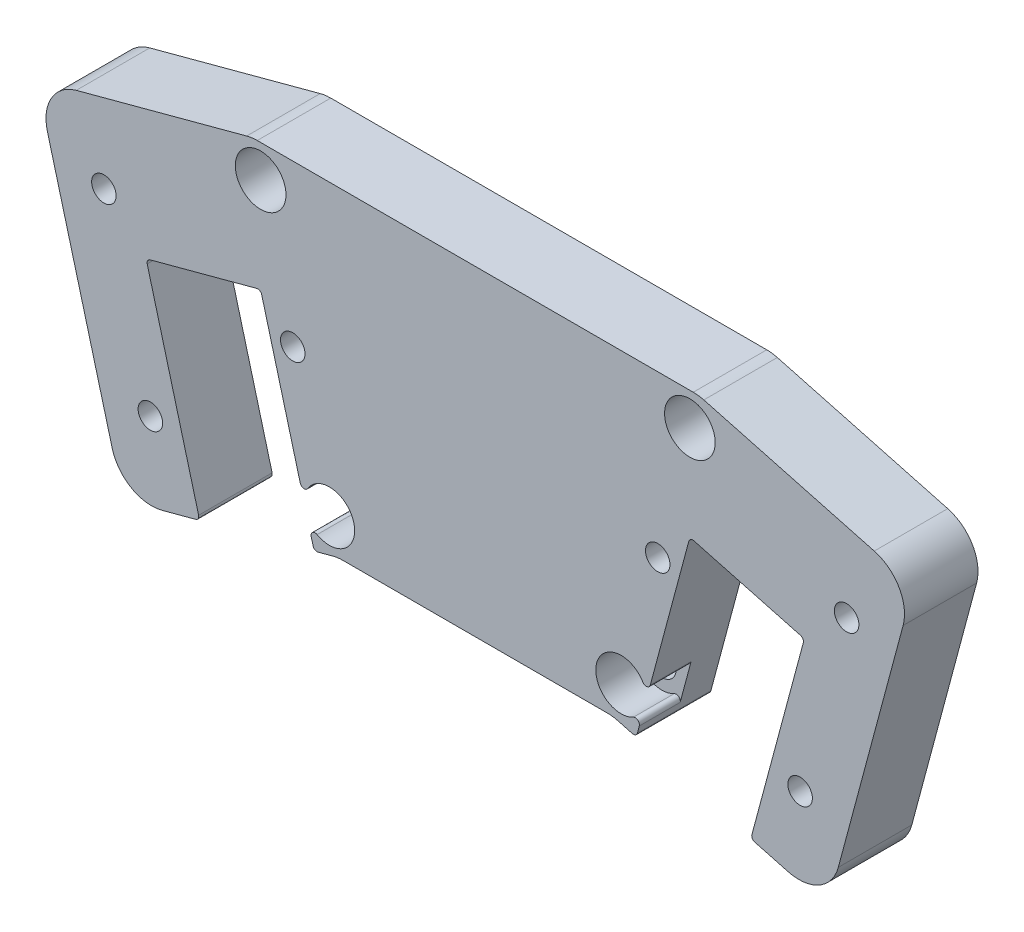
SolidWorks part; units mm, degrees
material "ABS"
ref_plane "前视基准面" through (0, 0, 0) normal (0, 0, 1) x (1, 0, 0)
ref_plane "上视基准面" through (0, 0, 0) normal (0, 1, 0) x (1, 0, 0)
ref_plane "右视基准面" through (0, 0, 0) normal (1, 0, 0) x (0, 0, -1)
other "Configuration Table"
sketch "草图1" plane through (0, 0, 0) normal (0, 0, 1) x (1, 0, 0)
  line L0 (-27.3543, 0) -> (27.3543, 0)
  line L4 (16.8283, -39.2834) -> (-16.8283, -39.2834)
  line L8 (0, 0) -> (0, -39.2834) construction
  line L9 (-43.1642, -46.3401) -> (-16.8283, -39.2834)
  line L10 (-53.6901, -7.0567) -> (-49.7212, -21.8688)
  line L11 (-27.3543, 0) -> (-53.6901, -7.0567)
  line L12 (-60, -29.8724) -> (-60, 12.6276) construction
  line L13 (-60, -29.8724) -> (-85.8724, 3.8452) construction
  line L14 (-60, -29.8724) -> (-17.5, -29.8724) construction
  line L15 (-60, -29.8724) -> (-34.1276, -63.5899) construction
  line L16 (-27.3543, 0) -> (-16.8283, -39.2834) construction
  line L17 (-60.0465, -29.8118) -> (-22.0913, -19.6417) construction
  line L18 (-49.7212, -21.8688) -> (-30.4027, -16.6924) construction
  line L19 (-52.8271, -10.2776) -> (-44.0272, -43.1191) construction
  line L20 (-47.1331, -31.528) -> (-27.8145, -26.3516) construction
  line L27 (-30.4027, -16.6924) -> (-27.8145, -26.3516) construction
  line L30 (-47.1331, -31.528) -> (-43.1642, -46.3401)
  line L31 (27.3543, 0) -> (53.6901, -7.0567)
  line L32 (53.6901, -7.0567) -> (49.7212, -21.8688)
  line L33 (49.7212, -21.8688) -> (30.4027, -16.6924) construction
  line L38 (30.4027, -16.6924) -> (27.8145, -26.3516) construction
  line L43 (47.1331, -31.528) -> (27.8145, -26.3516) construction
  line L44 (47.1331, -31.528) -> (43.1642, -46.3401)
  line L45 (43.1642, -46.3401) -> (16.8283, -39.2834)
  line L46 (-52.8271, -10.2776) -> (-45.0997, -8.2071) construction
  line L47 (-45.0997, -8.2071) -> (-18.8116, -13.5865) construction
  line L48 (-18.8116, -13.5865) -> (-16.2234, -23.2458) construction
  line L49 (-17.5175, -18.4162) -> (-22.0913, -19.6417) construction
  line L50 (-44.0272, -43.1191) -> (-36.2998, -41.0486) construction
  line L51 (-36.2998, -41.0486) -> (-16.2234, -23.2458) construction
  line L52 (-45.4786, -14.5203) -> (-39.7846, -35.7707) construction
  line L53 (-49.7212, -21.8688) -> (-47.1331, -31.528)
  line L54 (-33.7464, -43.8166) -> (-40.3035, -19.3453)
  line L55 (-40.3035, -19.3453) -> (-26.2832, -15.5885)
  line L56 (-26.2832, -15.5885) -> (-19.7261, -40.0599)
  line L57 (49.7212, -21.8688) -> (47.1331, -31.528)
  line L58 (33.7464, -43.8166) -> (40.3035, -19.3453)
  line L59 (40.3035, -19.3453) -> (26.2832, -15.5885)
  line L60 (26.2832, -15.5885) -> (19.7261, -40.0599)
  line L62 (-24.5925, -21.9556) -> (-21.5253, -22.7775) construction
  line L63 (-21.5253, -22.7775) -> (-19.2799, -20.5321) construction
  line L64 (-19.2799, -20.5321) -> (-20.1018, -17.4649) construction
  line L65 (-20.1018, -17.4649) -> (-23.169, -16.643) construction
  line L66 (-23.169, -16.643) -> (-25.4144, -18.8884) construction
  line L67 (-25.4144, -18.8884) -> (-24.5925, -21.9556) construction
  line L68 (-42.03, -38.016) -> (-38.9627, -38.8379) construction
  line L69 (-38.9627, -38.8379) -> (-36.7174, -36.5925) construction
  line L70 (-36.7174, -36.5925) -> (-37.5392, -33.5253) construction
  line L71 (-37.5392, -33.5253) -> (-40.6064, -32.7034) construction
  line L72 (-40.6064, -32.7034) -> (-42.8518, -34.9488) construction
  line L73 (-42.8518, -34.9488) -> (-42.03, -38.016) construction
  circle A0 centre (-60, -29.8724) radius 42.5 construction
  circle A1 centre (-85.8724, 3.8452) radius 1.75 construction
  circle A2 centre (-54.4526, 12.264) radius 1.75 construction
  circle A3 centre (-26.2825, -4) radius 1.75
  circle A4 centre (-17.8636, -35.4197) radius 1.75
  circle A5 centre (-34.1276, -63.5899) radius 1.75 construction
  circle A6 centre (-65.5474, -72.0088) radius 1.75 construction
  circle A7 centre (-93.7175, -55.7447) radius 1.75 construction
  circle A8 centre (-102.1364, -24.325) radius 1.75 construction
  circle A9 centre (-26.2825, -4) radius 3 construction
  circle A11 centre (-17.8636, -35.4197) radius 3 construction
  circle A12 centre (-26.2825, -4) radius 4 construction
  circle A13 centre (-17.8636, -35.4197) radius 4 construction
  circle A14 centre (17.8636, -35.4197) radius 1.75
  circle A15 centre (26.2825, -4) radius 1.75
  circle A16 centre (60, -29.8724) radius 42.5 construction
  circle A17 centre (-45.4786, -14.5203) radius 1.5
  circle A18 centre (-22.3472, -19.7103) radius 1.5
  circle A19 centre (-39.7846, -35.7707) radius 1.5
  circle A20 centre (45.4786, -14.5203) radius 1.5
  circle A21 centre (39.7846, -35.7707) radius 1.5
  circle A22 centre (22.3472, -19.7103) radius 1.5
  circle A23 centre (-22.3472, -19.7103) radius 2.75 construction
  circle A24 centre (-39.7846, -35.7707) radius 2.75 construction
  point P31 (-60, -29.8724)
  point P45 (-48.4272, -26.6984)
  dimension "D6" = 85
  dimension "D9" = 3.5
  dimension "D10" = 6
  dimension "D14" = 1
  dimension "D4" = 1
  dimension "D12" = 12
  dimension "D19" = 22
  dimension "D20" = 3
  dimension "D21" = 5
  dimension "D2" = 120
  dimension "D3" = 10
  dimension "D5" = 5.5
  dimension "D7" = 37.5
  dimension "D11" = 20
  dimension "D13" = 8
  dimension "D15" = 10
  dimension "D16" = 32
  dimension "D17" = 34
  dimension "D18" = 6
  dimension "D22" = 1
  dimension "D8" = 8
extrude "凸台-拉伸1" add sketch "草图1" along normal blind 9
fillet "圆角1" radius 5 8 edges at (27.3543, 0, 4.5) (53.6901, -7.0567, 4.5) (16.8283, -39.2834, 4.5) (43.1642, -46.3401, 4.5) (-43.1642, -46.3401, 4.5) (-16.8283, -39.2834, 4.5) (-27.3543, 0, 4.5) (-53.6901, -7.0567, 4.5)
sketch "草图2" plane through (0, 0, 0) normal (0, 0, -1) x (-1, 0, 0)
  line L0 (-45.4786, -14.5203) -> (-22.3472, -19.7103) construction
  line L1 (-42.4114, -15.3421) -> (-43.2332, -12.2749)
  line L2 (-43.2332, -12.2749) -> (-46.3005, -11.4531)
  line L3 (-46.3005, -11.4531) -> (-48.5458, -13.6984)
  line L4 (-48.5458, -13.6984) -> (-47.724, -16.7657)
  line L5 (-47.724, -16.7657) -> (-44.6567, -17.5875)
  line L6 (-44.6567, -17.5875) -> (-42.4114, -15.3421)
  line L7 (-22.3472, -19.7103) -> (-39.7846, -35.7707) construction
  line L8 (-39.7846, -35.7707) -> (-45.4786, -14.5203) construction
  line L10 (-31.7506, -22.2299) -> (-22.3472, -19.7103) construction
  line L12 (0, 0) -> (0, -39.2834) construction
  line L13 (-21.5253, -22.7775) -> (-19.2799, -20.5321)
  line L14 (-19.2799, -20.5321) -> (-20.1018, -17.4649)
  line L15 (-20.1018, -17.4649) -> (-23.169, -16.643)
  line L16 (-23.169, -16.643) -> (-25.4144, -18.8884)
  line L17 (-25.4144, -18.8884) -> (-24.5925, -21.9556)
  line L18 (-24.5925, -21.9556) -> (-21.5253, -22.7775)
  line L19 (-36.7174, -36.5925) -> (-37.5392, -33.5253)
  line L20 (-37.5392, -33.5253) -> (-40.6064, -32.7034)
  line L21 (-40.6064, -32.7034) -> (-42.8518, -34.9488)
  line L22 (-42.8518, -34.9488) -> (-42.03, -38.016)
  line L23 (-42.03, -38.016) -> (-38.9627, -38.8379)
  line L24 (-38.9627, -38.8379) -> (-36.7174, -36.5925)
  line L44 (-16.1701, -39.2834) -> (16.1701, -39.2834) construction
  line L45 (38.9627, -38.8379) -> (36.7174, -36.5925)
  line L46 (42.03, -38.016) -> (38.9627, -38.8379)
  line L47 (42.8518, -34.9488) -> (42.03, -38.016)
  line L48 (40.6064, -32.7034) -> (42.8518, -34.9488)
  line L49 (37.5392, -33.5253) -> (40.6064, -32.7034)
  line L50 (36.7174, -36.5925) -> (37.5392, -33.5253)
  line L51 (24.5925, -21.9556) -> (21.5253, -22.7775)
  line L52 (25.4144, -18.8884) -> (24.5925, -21.9556)
  line L53 (23.169, -16.643) -> (25.4144, -18.8884)
  line L54 (20.1018, -17.4649) -> (23.169, -16.643)
  line L55 (19.2799, -20.5321) -> (20.1018, -17.4649)
  line L56 (21.5253, -22.7775) -> (19.2799, -20.5321)
  line L57 (44.6567, -17.5875) -> (42.4114, -15.3421)
  line L58 (47.724, -16.7657) -> (44.6567, -17.5875)
  line L59 (48.5458, -13.6984) -> (47.724, -16.7657)
  line L60 (46.3005, -11.4531) -> (48.5458, -13.6984)
  line L61 (43.2332, -12.2749) -> (46.3005, -11.4531)
  line L62 (42.4114, -15.3421) -> (43.2332, -12.2749)
  circle A0 centre (-45.4786, -14.5203) radius 2.75 construction
  circle A1 centre (-22.3472, -19.7103) radius 2.75 construction
  circle A2 centre (-39.7846, -35.7707) radius 2.75 construction
  circle A3 centre (-22.3472, -19.7103) radius 1.5 construction
  circle A4 centre (-45.4786, -14.5203) radius 1.5 construction
  circle A5 centre (-39.7846, -35.7707) radius 1.5 construction
  dimension "D1" = 5.5
extrude "切除-拉伸1" cut sketch "草图2" against normal blind 3.5
sketch "草图5" plane through (0, 0, 9) normal (0, 0, 1) x (1, 0, 0)
  circle A0 centre (-26.2825, -4) radius 3.1
  circle A1 centre (-17.8636, -35.4197) radius 3.1
  circle A2 centre (17.8636, -35.4197) radius 3.1
  circle A3 centre (26.2825, -4) radius 3.1
  dimension "D1" = 6.2
extrude "切除-拉伸2" cut sketch "草图5" against normal offset from surface (5 mm away) 4 up to face at (39.7846, -35.7707, 0)
fillet "圆角2" radius 0.5 12 edges at (20.9635, -35.4418, 6.5) (20.5592, -36.9506, 6.5) (-20.9635, -35.4418, 6.5) (-20.5592, -36.9506, 6.5) (33.7464, -43.8166, 4.5) (40.3035, -19.3453, 4.5) (26.2832, -15.5885, 4.5) (19.7261, -40.0599, 4.5) (-19.7261, -40.0599, 4.5) (-40.3035, -19.3453, 4.5) (-33.7464, -43.8166, 4.5) (-26.2832, -15.5885, 4.5)
